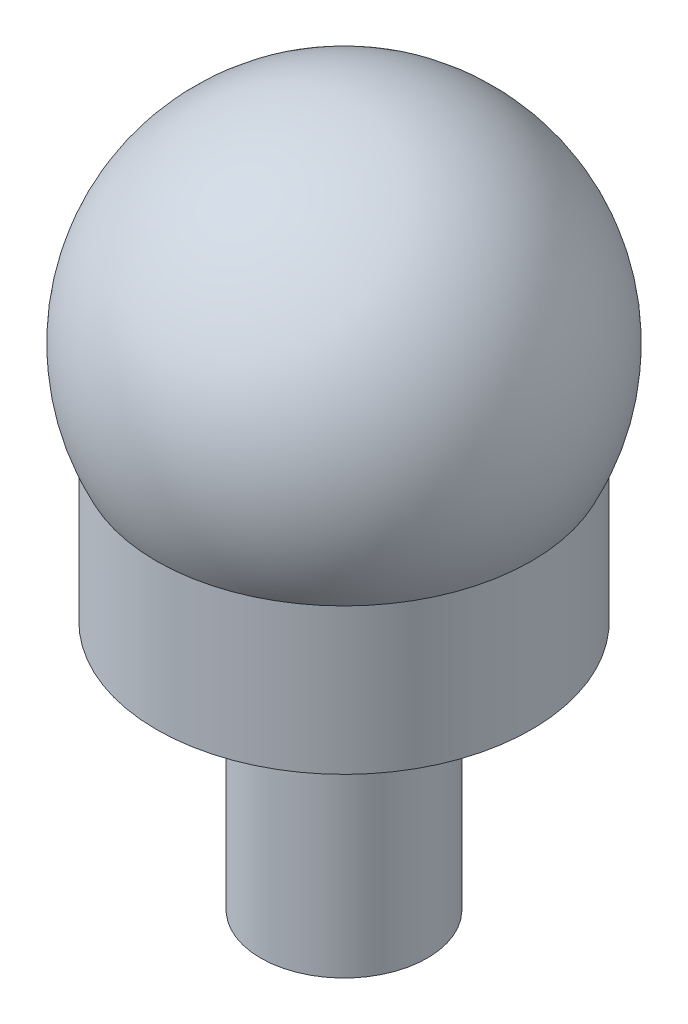
SolidWorks part; units mm, degrees
ref_plane "Front Plane" through (0, 0, 0) normal (0, 0, 1) x (1, 0, 0)
ref_plane "Top Plane" through (0, 0, 0) normal (0, 1, 0) x (1, 0, 0)
ref_plane "Right Plane" through (0, 0, 0) normal (1, 0, 0) x (0, 0, -1)
sketch "Sketch1" plane through (0, 0, 0) normal (0, 1, 0) x (1, 0, 0)
  circle A0 centre (0, 0) radius 4
extrude "Boss-Extrude1" add sketch "Sketch1" along normal blind 12
sketch "Sketch3" plane through (0, 12, 0) normal (0, 1, 0) x (1, 0, 0)
  circle A0 centre (0, 0) radius 9
extrude "Boss-Extrude2" add sketch "Sketch3" along normal blind 7
sketch "Sketch4" plane through (0, 0, 0) normal (0, 0, 1) x (1, 0, 0)
  line L0 (9, 19) -> (-9, 19) construction
  line L1 (0, 28.1194) -> (0, 19)
  line L2 (0, 19) -> (9, 19)
  line L3 (0, 28.1194) -> (0, 33.6488)
  arc A0 (9, 19) -> (0, 33.6488) centre (0, 23.5597) ccw
revolve "Revolve2" add sketch "Sketch4" angle 360 about L1
